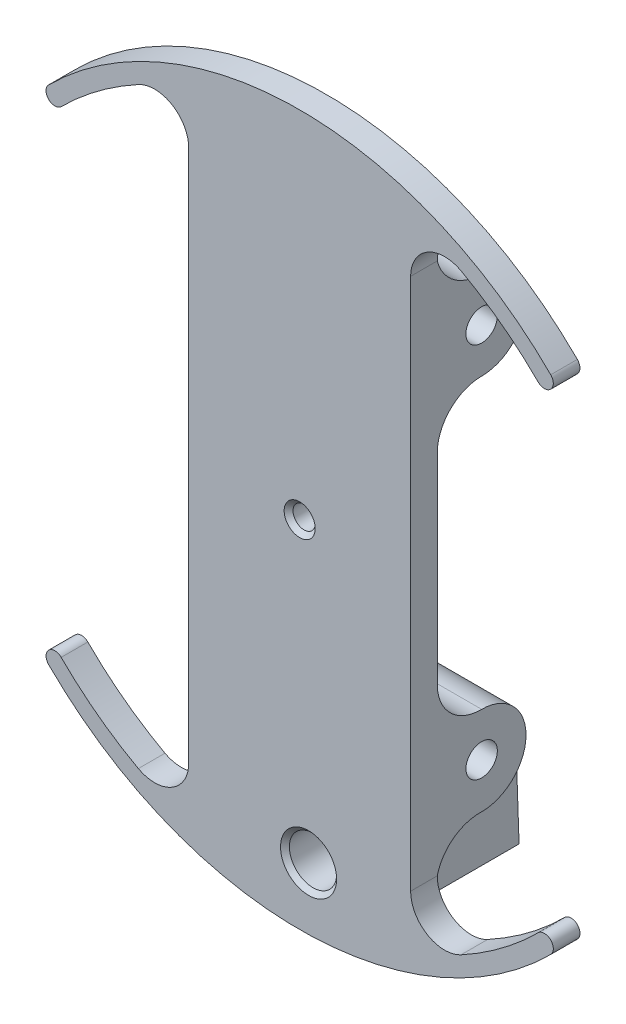
SolidWorks part; units mm, degrees
ref_plane "Front Plane" through (0, 0, 0) normal (0, 0, 1) x (1, 0, 0)
ref_plane "Top Plane" through (0, 0, 0) normal (0, 1, 0) x (1, 0, 0)
ref_plane "Right Plane" through (0, 0, 0) normal (1, 0, 0) x (0, 0, -1)
sketch "Sketch3" plane through (0, 0, 0) normal (0, 0, 1) x (1, 0, 0)
  line L0 (-35.921, -35.921) -> (-34.125, -34.125) construction
  line L1 (-15.875, -38.1) -> (0, -38.1) construction
  line L2 (-15.875, -38.1) -> (-15.875, 38.1)
  line L3 (-15.875, 38.1) -> (0, 38.1) construction
  line L4 (15.875, -38.1) -> (15.875, 38.1)
  line L5 (-15.875, -38.1) -> (15.875, 38.1) construction
  line L6 (-15.875, 38.1) -> (15.875, -38.1) construction
  line L7 (35.921, -35.921) -> (34.125, -34.125) construction
  line L8 (0, -50.8) -> (0, 50.8) construction
  line L9 (0, 38.1) -> (15.875, 38.1) construction
  line L10 (0, -38.1) -> (15.875, -38.1) construction
  line L11 (-34.125, -34.125) -> (-15.875, -15.875) construction
  line L12 (34.125, 34.125) -> (35.921, 35.921) construction
  line L13 (-15.875, -15.875) -> (0, 0) construction
  line L14 (15.875, -15.875) -> (0, 0) construction
  line L15 (-34.125, 34.125) -> (-35.921, 35.921) construction
  line L16 (34.125, -34.125) -> (15.875, -15.875) construction
  line L17 (0, 0) -> (-15.875, 15.875) construction
  line L18 (0, 0) -> (15.875, 15.875) construction
  line L19 (-15.875, 15.875) -> (-34.125, 34.125) construction
  line L20 (15.875, 15.875) -> (34.125, 34.125) construction
  arc A0 (-35.921, -35.921) -> (35.921, -35.921) centre (0, 0) ccw
  arc A1 (-34.125, -34.125) -> (-23.0827, -42.3818) centre (0, 0) ccw
  arc A2 (-15.875, 38.1) -> (-23.0827, 42.3818) centre (-20.7507, 38.1) ccw
  arc A3 (15.875, 38.1) -> (23.0827, 42.3818) centre (20.7507, 38.1) cw
  arc A4 (-15.875, -38.1) -> (-23.0827, -42.3818) centre (-20.7507, -38.1) cw
  arc A5 (15.875, -38.1) -> (23.0827, -42.3818) centre (20.7507, -38.1) ccw
  arc A6 (-35.921, 35.921) -> (-35.921, -35.921) centre (0, 0) ccw construction
  circle A7 centre (0, 0) radius 50.8 construction
  arc A8 (-34.125, 34.125) -> (-34.125, -34.125) centre (0, 0) ccw construction
  circle A9 centre (0, 0) radius 48.26 construction
  arc A10 (34.125, -34.125) -> (34.125, 34.125) centre (0, 0) ccw construction
  arc A11 (34.125, 34.125) -> (23.0827, 42.3818) centre (0, 0) ccw
  arc A12 (35.921, -35.921) -> (35.921, 35.921) centre (0, 0) ccw construction
  arc A13 (35.921, 35.921) -> (-35.921, 35.921) centre (0, 0) ccw
  arc A14 (0, 48.26) -> (-23.0827, 42.3818) centre (0, 0) ccw construction
  arc A15 (-23.0827, 42.3818) -> (-34.125, 34.125) centre (0, 0) ccw
  arc A16 (23.0827, 42.3818) -> (0, 48.26) centre (0, 0) ccw construction
  arc A17 (-23.0827, -42.3818) -> (0, -48.26) centre (0, 0) ccw construction
  arc A18 (23.0827, -42.3818) -> (34.125, -34.125) centre (0, 0) ccw
  arc A19 (0, -48.26) -> (23.0827, -42.3818) centre (0, 0) ccw construction
  arc A20 (-35.921, 35.921) -> (-34.125, 34.125) centre (-35.023, 35.023) ccw
  arc A21 (34.125, 34.125) -> (35.921, 35.921) centre (35.023, 35.023) ccw
  arc A22 (-35.921, -35.921) -> (-34.125, -34.125) centre (-35.023, -35.023) cw
  arc A23 (34.125, -34.125) -> (35.921, -35.921) centre (35.023, -35.023) cw
  point P0 (0, 0)
  point P13 (0, 0)
  point P16 (0, 0)
  point P18 (0, 0)
  dimension "D3" = 2.54
  dimension "D6" = 101.6
  dimension "D1" = 76.2
  dimension "D2" = 31.75
  dimension "D4" = 45
  dimension "D5" = 45
extrude "Main Body" add sketch "Sketch3" along normal blind 3.81
sketch "Sketch5" plane through (15.875, 0, 0) normal (1, 0, 0) x (0, 0, -1)
  line L0 (0, 26.9938) -> (0, -26.9938)
  line L1 (0, -38.1) -> (0, 38.1) construction
  line L2 (0, 26.9938) -> (6.35, 26.9939) construction
  line L3 (6.35, 26.9939) -> (6.35, -26.9938) construction
  line L4 (6.35, -26.9938) -> (0, -26.9938) construction
  line L5 (0, 38.1) -> (0, 14.2939)
  line L6 (0, -14.2939) -> (0, -38.1)
  circle A0 centre (-0.0451, 26.9938) radius 0.0451
  arc A2 (6.35, 20.6439) -> (6.3413, 33.3438) centre (6.35, 26.9939) ccw
  arc A3 (6.0778, -33.338) -> (6.2617, -20.6445) centre (6.35, -26.9938) ccw
  arc A4 (6.35, 20.6439) -> (0, 14.2939) centre (6.3675, 14.2763) ccw
  arc A5 (6.3413, 33.3438) -> (0, 38.1) centre (6.1542, 39.6999) cw
  arc A6 (6.35, -20.6438) -> (0, -14.2939) centre (6.2623, -14.3815) cw
  arc A7 (6.35, -33.3439) -> (0, -38.1) centre (6.0797, -39.6) ccw
  arc A8 (6.3413, 33.3438) -> (0, 26.9938) centre (6.35, 26.9939) ccw construction
  arc A9 (0, 26.9938) -> (6.35, 20.6439) centre (6.35, 26.9939) ccw construction
  arc A10 (6.2617, -20.6445) -> (0, -26.9938) centre (6.35, -26.9938) ccw construction
  arc A11 (0, -26.9938) -> (6.0778, -33.338) centre (6.35, -26.9938) ccw construction
  point P5 (0, 0)
  line M6 (0, -38.1) -> (0, 38.1)
  dimension "D1" = 53.9877
  dimension "D2" = 6.35
  dimension "D3" = 12.7
  dimension "D4" = 12.7
extrude "Bosses for screws" add sketch "Sketch5" against normal up to surface (31.75 mm away) contours A2 A5 L0 A4 M6 | A7 A3 A6 L6 M6 up to face at (-15.875, 0, 1.905)
sketch "Sketch18" plane through (0, 0, 0) normal (0, 0, -1) x (-1, 0, 0)
  line L1 (-10.4707, -49.4103) -> (9.3869, -49.4103)
  line L2 (-10.4707, -49.4103) -> (-10.4707, -34.1772)
  line L3 (-10.4707, -34.1772) -> (9.3869, -34.1772)
  line L4 (9.3869, -49.4103) -> (9.3869, -34.1772)
extrude "Boss-Extrude6" [suppressed] add sketch "Sketch18" along normal blind 25.4
hole_wizard "#8 Clearance Hole for screws" positions "Sketch8" profile "Sketch7" hole size "#8" standard "ANSI Inch" end condition through all
sketch "Sketch8" plane through (15.875, 0, 0) normal (1, 0, 0) x (0, 0, -1)
  point P7 (6.35, 26.9939)
  point P10 (6.35, -26.8934)
sketch "Sketch7" plane through (15.875, 26.9939, -6.35) normal (0, 1, 0) x (0, 0, -1)
  line L0 (0, 0) -> (0, 52.168)
  line L1 (0, 52.168) -> (2.2479, 52.168)
  line L2 (2.2479, 52.168) -> (2.2479, 0)
  line L5 (2.2479, 0) -> (0, 0)
  line L11 (0, -6.35) -> (0, 107.95) construction
  dimension "Thru Hole Dia." = 4.4958
  dimension "Thru Hole Depth" = 52.168
hole_wizard "1/8 (0.125) Diameter let down hole" positions "Sketch9" profile "Sketch10" hole size "1/8" standard "ANSI Inch" end condition up to next
sketch "Sketch9" plane through (0, 0, 0) normal (0, 0, -1) x (-1, 0, 0)
  point P0 (0, 0)
sketch "Sketch10" plane through (0, 0, 0) normal (1, 0, 0) x (0, 1, 0)
  line L0 (0, 0) -> (0, 3.81)
  line L1 (0, 3.81) -> (2.2225, 3.81)
  line L2 (1.5875, 3.175) -> (1.5875, 0.635)
  line L3 (1.5875, 0.635) -> (2.2225, 0)
  line L5 (2.2225, 0) -> (0, 0)
  line L6 (-1.5875, 0.635) -> (-2.2225, 0) construction
  line L7 (2.2225, 3.81) -> (1.5875, 3.175)
  line L8 (-2.2225, 3.81) -> (-1.5875, 3.175) construction
  line L11 (0, -6.35) -> (0, 107.95) construction
  dimension "Thru Hole Dia." = 3.175
  dimension "Thru Hole Depth" = 3.81
  dimension "Near C'Sink Dia." = 4.445
  dimension "Near C'Sink Angle" = 90
  dimension "Far C'Sink Dia." = 4.445
  dimension "Far C'Sink Angle" = 90
sketch "Sketch19" plane through (0, 0, 0) normal (0, 0, -1) x (-1, 0, 0)
  line L0 (12.7, -38.735) -> (2.921, -38.735)
  line L1 (-1.27, 0) -> (0, 0) construction
  line L4 (2.921, -38.735) -> (2.921, -45.085)
  line L6 (-1.27, -41.91) -> (-1.27, 0) construction
  line L12 (12.7, -48.26) -> (-7.62, -48.26)
  line L13 (-7.62, -48.26) -> (-7.62, -35.56)
  line L14 (-7.62, -35.56) -> (12.7, -35.56)
  line L16 (12.7, -38.735) -> (12.7, -35.56)
  line L18 (12.7, -45.085) -> (12.7, -48.26)
  line L25 (2.921, -45.085) -> (12.7, -45.085)
  line L26 (-1.27, -41.91) -> (2.921, -41.91) construction
  circle A1 centre (-1.27, -41.91) radius 3.3782
  dimension "D1" = 4.191
  dimension "D2" = 3.175
  dimension "D3" = 20.32
  dimension "D4" = 6.35
  dimension "D5" = 3.175
  dimension "D6" = 6.35
  dimension "D7" = 12.7
  dimension "D8" = 41.91
  dimension "D9" = 1.27
extrude "Switch holder body" add sketch "Sketch19" along normal up to surface (19.9395 mm away)
hole_wizard "1/4 QR pin hole" positions "Sketch23" profile "Sketch24" hole size "1/4" standard "ANSI Inch" end condition through all
sketch "Sketch23" plane through (0, 0, 3.81) normal (0, 0, 1) x (1, 0, 0)
  line L16 (-12.7, -38.735) -> (-2.921, -38.735)
  line L17 (-2.921, -38.735) -> (-2.921, -45.085)
  line L18 (-2.921, -45.085) -> (-12.7, -45.085)
  line L19 (-12.7, -45.085) -> (-12.7, -48.26)
  line L20 (-12.7, -48.26) -> (7.62, -48.26)
  line L21 (7.62, -48.26) -> (7.62, -35.56)
  line L22 (7.62, -35.56) -> (-12.7, -35.56)
  line L23 (-12.7, -35.56) -> (-12.7, -38.735)
  line L24 (-12.7, -38.735) -> (-2.921, -38.735)
  line L25 (-2.921, -38.735) -> (-2.921, -45.085)
  line L26 (-2.921, -45.085) -> (-12.7, -45.085)
  line L27 (-12.7, -45.085) -> (-12.7, -48.26)
  line L28 (-12.7, -48.26) -> (7.62, -48.26)
  line L29 (7.62, -48.26) -> (7.62, -35.56)
  line L30 (7.62, -35.56) -> (-12.7, -35.56)
  line L31 (-12.7, -35.56) -> (-12.7, -38.735)
  circle A2 centre (1.27, -41.91) radius 3.3782
  circle A3 centre (1.27, -41.91) radius 3.3782
  point P39 (1.27, -41.91)
  dimension "D1" = 0
  dimension "D2" = 0
sketch "Sketch24" plane through (1.27, -41.91, 3.81) normal (1, 0, 0) x (0, -1, 0)
  line L0 (0, 0) -> (0, 23.9425)
  line L1 (0, 23.9425) -> (3.3782, 23.9425)
  line L2 (3.3782, 23.9425) -> (3.3782, 0.635)
  line L3 (3.3782, 0.635) -> (4.0132, 0)
  line L5 (4.0132, 0) -> (0, 0)
  line L6 (-3.3782, 0.635) -> (-4.0132, 0) construction
  line L11 (0, -6.35) -> (0, 107.95) construction
  dimension "Thru Hole Dia." = 6.7564
  dimension "Thru Hole Depth" = 23.9425
  dimension "Near C'Sink Dia." = 8.0264
  dimension "Near C'Sink Angle" = 90
sketch "Sketch25" plane through (-2.921, 0, 0) normal (-1, 0, 0) x (0, 0, 1)
  circle A2 centre (-7.285, -41.935) radius 1.1 construction
  circle A3 centre (-7.285, -41.935) radius 1.1 construction
  circle A4 centre (-7.285, -41.935) radius 1.862
  dimension "D4" = 0.762
extrude "plunger hole" cut sketch "Sketch25" against normal blind 2.54
sketch "Sketch33" plane through (-2.921, 0, 0) normal (-1, 0, 0) x (0, 0, 1)
  line L0 (-19.7177, -38.735) -> (0, -38.735) construction
  line L1 (-10.485, -45.135) -> (-4.085, -45.135)
  line L2 (-10.485, -45.135) -> (-10.485, -38.735)
  line L3 (-10.485, -38.735) -> (-4.085, -38.735)
  line L4 (-4.085, -45.135) -> (-4.085, -38.735)
  line L5 (-10.485, -45.135) -> (-4.085, -38.735) construction
  line L6 (-10.485, -38.735) -> (-4.085, -45.135) construction
  point P0 (-7.285, -41.935)
extrude "switch body clearance" cut sketch "Sketch33" against normal blind 0.6502
sketch "Sketch28" plane through (0, -48.26, 0) normal (0, -1, 0) x (-1, 0, 0)
  line L0 (9.571, 5.35) -> (9.571, 5.05) construction
hole_wizard "#2 Clearance Hole1" positions "Sketch29" profile "Sketch30" hole size "#2" standard "ANSI Inch"
sketch "Sketch29" plane through (0, -48.26, 0) normal (0, -1, 0) x (-1, 0, 0)
  line L0 (9.571, 5.35) -> (9.571, 5.05) construction
  point P0 (9.571, 14.7)
  point P13 (9.571, 5.2)
sketch "Sketch30" plane through (-9.571, -48.26, -14.7) normal (1, 0, 0) x (0, 0, -1)
  line L0 (0, 0) -> (0, 3.175)
  line L1 (0, 3.175) -> (1.2192, 3.175)
  line L2 (1.2192, 3.175) -> (1.2192, 0)
  line L5 (1.2192, 0) -> (0, 0)
  line L11 (0, -6.35) -> (0, 107.95) construction
  dimension "Thru Hole Dia." = 2.4384
  dimension "Thru Hole Depth" = 3.175
hole_wizard "Tap Drill for #2-56 Tap1" positions "Sketch31" profile "Sketch32" hole size "#2-56" standard "ANSI Inch"
sketch "Sketch31" plane through (0, -48.26, 0) normal (0, -1, 0) x (-1, 0, 0)
  line L0 (9.571, 5.35) -> (9.571, 5.05) construction
  point P0 (9.571, 14.7)
  point P3 (9.571, 5.2)
sketch "Sketch32" plane through (-9.571, -48.26, -14.7) normal (1, 0, 0) x (0, 0, -1)
  line L0 (0, 0) -> (0, 12.7)
  line L1 (0, 12.7) -> (0.889, 12.7)
  line L2 (0.889, 12.7) -> (0.889, 0)
  line L5 (0.889, 0) -> (0, 0)
  line L11 (0, -6.35) -> (0, 107.95) construction
  dimension "Thru Hole Dia." = 1.778
  dimension "Thru Hole Depth" = 12.7
